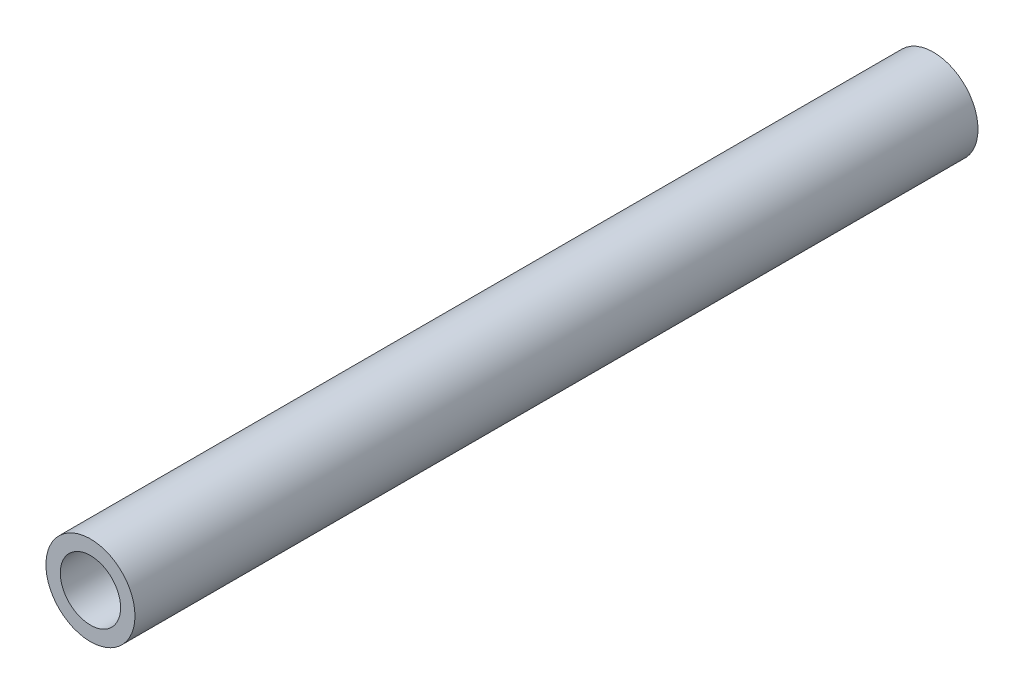
SolidWorks part; units mm, degrees
ref_plane "Front Plane" through (0, 0, 0) normal (0, 0, 1) x (1, 0, 0)
ref_plane "Top Plane" through (0, 0, 0) normal (0, 1, 0) x (1, 0, 0)
ref_plane "Right Plane" through (0, 0, 0) normal (1, 0, 0) x (0, 0, -1)
sketch "Sketch1" plane through (0, 0, 0) normal (0, 0, 1) x (1, 0, 0)
  circle A0 centre (0, 0) radius 6.45
  circle A1 centre (0, 0) radius 9.525
  dimension "D1" = 12.9
  dimension "D2" = 19.05
extrude "Boss-Extrude1" add sketch "Sketch1" along normal blind 180.34
